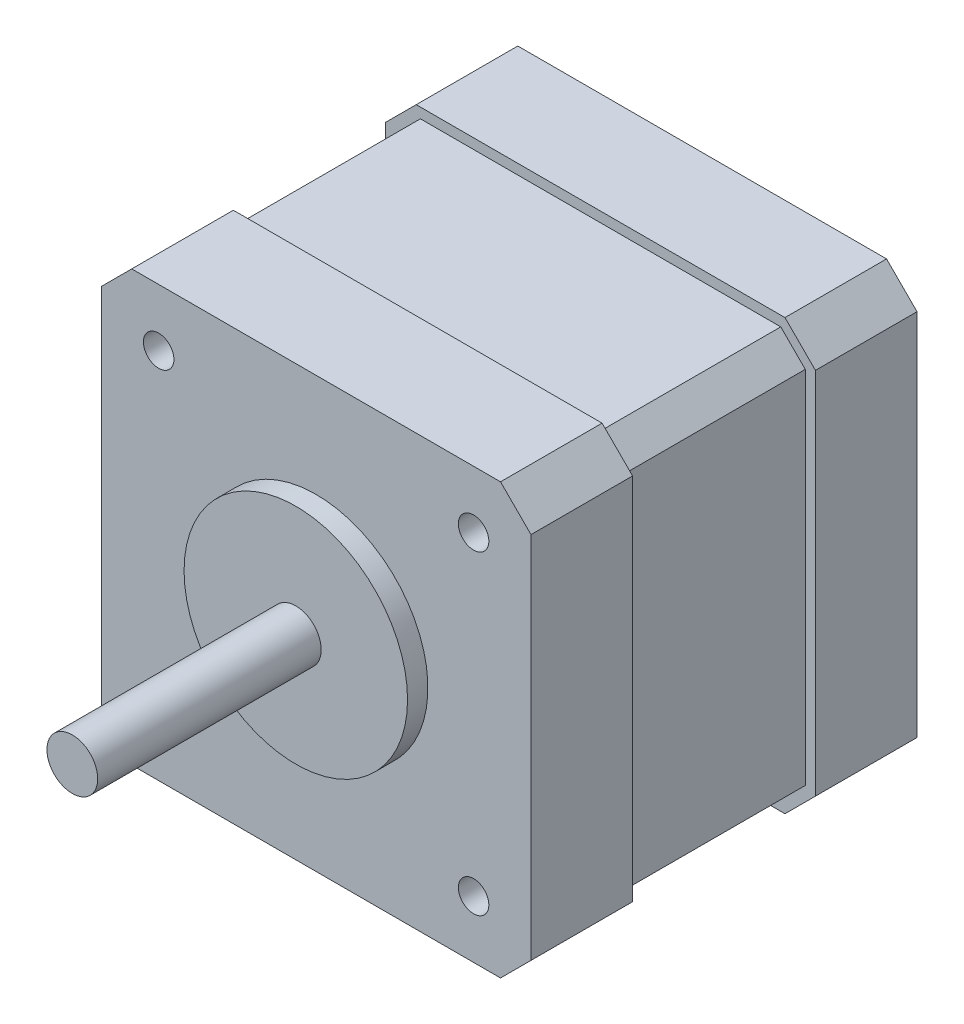
SolidWorks part; units mm, degrees
ref_plane "Спереди" through (0, 0, 0) normal (0, 0, 1) x (1, 0, 0)
ref_plane "Сверху" through (0, 0, 0) normal (0, 1, 0) x (1, 0, 0)
ref_plane "Справа" through (0, 0, 0) normal (1, 0, 0) x (0, 0, -1)
sketch "Эскиз1" plane through (0, 0, 0) normal (0, 0, 1) x (1, 0, 0)
  line L0 (-32.7678, -16.5362) -> (-32.7678, 19.7638)
  line L1 (-29.7678, 22.7638) -> (6.5322, 22.7638)
  line L2 (9.5322, 19.7638) -> (9.5322, -16.5362)
  line L3 (6.5322, -19.5362) -> (-29.7678, -19.5362)
  line L4 (-32.7678, 19.7638) -> (-29.7678, 22.7638)
  line L5 (6.5322, 22.7638) -> (9.5322, 19.7638)
  line L6 (9.5322, -16.5362) -> (6.5322, -19.5362)
  line L7 (-29.7678, -19.5362) -> (-32.7678, -16.5362)
  point P0 (-32.7678, -19.5362)
  point P1 (-32.7678, 22.7638)
  point P2 (9.5322, 22.7638)
  point P3 (9.5322, -19.5362)
extrude "Бобышка-Вытянуть1" add sketch "Эскиз1" along normal blind 10
sketch "Эскиз2" plane through (0, 0, 10) normal (0, 0, 1) x (1, 0, 0)
  circle A0 centre (-11.6178, 1.6138) radius 11
  dimension "D1" = 22
extrude "Бобышка-Вытянуть2" add sketch "Эскиз2" along normal blind 2
sketch "Эскиз3" plane through (0, 0, 12) normal (0, 0, 1) x (1, 0, 0)
  circle A0 centre (-11.6178, 1.6138) radius 2.5
extrude "Бобышка-Вытянуть3" add sketch "Эскиз3" along normal blind 22
sketch "Эскиз6" plane through (0, 0, 0) normal (0, 0, -1) x (-1, 0, 0)
  line L2 (11.6178, 21.7638) -> (-6.118, 21.7638)
  line L4 (-8.5322, 19.3496) -> (-8.5322, -16.122)
  line L5 (-6.5322, -19.5362) -> (-9.5322, -16.5362) construction
  line L6 (-6.118, -18.5362) -> (29.3535, -18.5362)
  line L7 (32.7678, -16.5362) -> (29.7678, -19.5362) construction
  line L9 (31.7678, -16.122) -> (31.7678, 19.3496)
  line L10 (29.7678, 22.7638) -> (32.7678, 19.7638) construction
  line L11 (11.6178, 21.7638) -> (29.3535, 21.7638)
  line L12 (-8.5322, -16.122) -> (-6.118, -18.5362)
  line L13 (-8.5322, 19.3496) -> (-6.118, 21.7638)
  line L14 (-9.5322, 19.7638) -> (-6.5322, 22.7638) construction
  line L15 (29.3535, 21.7638) -> (31.7678, 19.3496)
  line L16 (29.3535, -18.5362) -> (31.7678, -16.122)
  dimension "D1" = 1
  dimension "D2" = 1
  dimension "D3" = 1
  dimension "D4" = 1
extrude "Бобышка-Вытянуть4" add sketch "Эскиз6" along normal blind 18
sketch "Эскиз7" plane through (0, 0, -18) normal (0, 0, 1) x (1, 0, 0)
  line L0 (-32.7678, -16.5362) -> (-32.7678, 19.7638)
  line L1 (-29.7678, 22.7638) -> (6.5322, 22.7638)
  line L2 (9.5322, 19.7638) -> (9.5322, -16.5362)
  line L3 (6.5322, -19.5362) -> (-29.7678, -19.5362)
  line L4 (-32.7678, 19.7638) -> (-29.7678, 22.7638)
  line L5 (6.5322, 22.7638) -> (9.5322, 19.7638)
  line L6 (9.5322, -16.5362) -> (6.5322, -19.5362)
  line L7 (-29.7678, -19.5362) -> (-32.7678, -16.5362)
  point P0 (-32.7678, -19.5362)
  point P1 (-32.7678, 22.7638)
  point P2 (9.5322, 22.7638)
  point P3 (9.5322, -19.5362)
extrude "Бобышка-Вытянуть5" add sketch "Эскиз7" against normal blind 10
sketch "Эскиз4" plane through (0, 0, 10) normal (0, 0, 1) x (1, 0, 0)
  circle A0 centre (-27.1178, 17.1138) radius 1.5
  circle A1 centre (3.8822, 17.1138) radius 1.5
  circle A2 centre (3.8822, -13.8862) radius 1.5
  circle A3 centre (-27.1178, -13.8862) radius 1.5
  point P0 (3.8822, -13.8862)
  point P1 (-27.1178, -13.8862)
  point P14 (-27.1178, 17.1138)
  point P23 (3.8822, 17.1138)
  dimension "D1" = 31
  dimension "D2" = 31
extrude "Вырез-Вытянуть1" cut sketch "Эскиз4" against normal blind 46.5
sketch "Эскиз5" plane through (0, 0, -28) normal (0, 0, -1) x (-1, 0, 0)
  circle A0 centre (11.6178, 1.6138) radius 2.5
extrude "Вырез-Вытянуть2" cut sketch "Эскиз5" against normal blind 1
